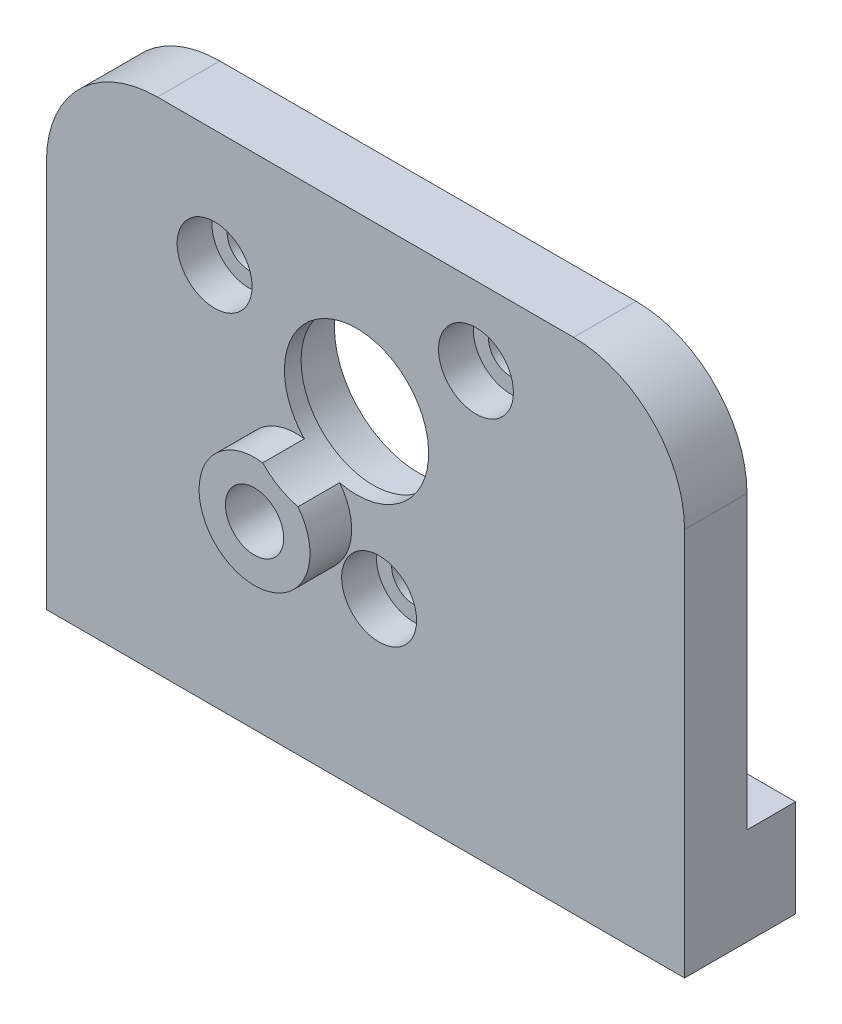
SolidWorks part; units mm, degrees
ref_plane "Front Plane" through (0, 0, 0) normal (0, 0, 1) x (1, 0, 0)
ref_plane "Top Plane" through (0, 0, 0) normal (0, 1, 0) x (1, 0, 0)
ref_plane "Right Plane" through (0, 0, 0) normal (1, 0, 0) x (0, 0, -1)
ref_plane "Plane1" through (0, 0, 4.5) normal (0, 0, 1) x (1, 0, 0)
sketch "Sketch1" plane through (0, 0, 4.5) normal (0, 0, 1) x (1, 0, 0)
  line L0 (-23, -18) -> (23, -18)
  line L1 (23, -18) -> (23, 18)
  line L2 (23, 18) -> (-23, 18)
  line L3 (-23, 18) -> (-23, -18)
extrude "Boss-Extrude1" add sketch "Sketch1" against normal blind 4.5
sketch "Sketch2" plane through (0, 0, 0) normal (0, 0, -1) x (-1, 0, 0)
  line L0 (-15, -11) -> (-15, -18)
  line L1 (-15, -18) -> (-23, -18)
  line L2 (-23, -18) -> (-23, -11)
  line L3 (-23, -11) -> (-15, -11)
extrude "Boss-Extrude2" add sketch "Sketch2" along normal blind 3.5
sketch "Sketch3" plane through (0, 0, 0) normal (0, 0, -1) x (-1, 0, 0)
  line L0 (23, -18) -> (15, -18)
  line L1 (15, -18) -> (15, -11)
  line L2 (15, -11) -> (23, -11)
  line L3 (23, -11) -> (23, -18)
extrude "Boss-Extrude3" add sketch "Sketch3" along normal blind 3.5
ref_plane "Plane2" through (0, -2, 0) normal (0, -1, 0) x (1, 0, 0)
sketch "Sketch4" plane through (0, -2, 0) normal (0, -1, 0) x (1, 0, 0)
  line L0 (-1, 7.5) -> (-5, 7.5)
  line L1 (-5, 7.5) -> (-5, 4.5)
  line L2 (-5, 4.5) -> (-1, 4.5)
  line L3 (-1, 4.5) -> (-1, 7.5)
  line L4 (-5, 7.5) -> (-5, 4.5) construction
revolve "Revolve1" add sketch "Sketch4" angle 360 about L4
hole_wizard "Ø1.7 (1.7) Diameter Hole1" positions "Sketch6" profile "Sketch5" hole size "Ø1.7" standard "ANSI Metric"
sketch "Sketch6" plane through (0, -18, 0) normal (0, -1, 0) x (-1, 0, 0)
  point P0 (0, -2.25)
sketch "Sketch5" plane through (0, -18, 2.25) normal (1, 0, 0) x (0, 0, -1)
  line L0 (0, 0) -> (0, 7.5107)
  line L1 (0, 7.5107) -> (0.85, 7)
  line L2 (0.85, 7) -> (0.85, 0)
  line L5 (0.85, 0) -> (0, 0)
  line L10 (0, 7.5107) -> (-0.85, 7) construction
  line L11 (0, -6.35) -> (0, 107.95) construction
  dimension "Hole Dia." = 1.7
  dimension "Hole Depth" = 7
  dimension "Drill Angle" = 118
hole_wizard "Ø2.5 (2.5) Diameter Hole1" positions "Sketch8" profile "Sketch7" hole size "Ø2.5" standard "ANSI Metric"
sketch "Sketch8" plane through (0, -18, 0) normal (0, -1, 0) x (-1, 0, 0)
  point P0 (-19, -0.5)
  point P1 (19, -0.5)
sketch "Sketch7" plane through (19, -18, 0.5) normal (1, 0, 0) x (0, 0, -1)
  line L0 (0, 0) -> (0, 6.7511)
  line L1 (0, 6.7511) -> (1.25, 6)
  line L2 (1.25, 6) -> (1.25, 0)
  line L5 (1.25, 0) -> (0, 0)
  line L10 (0, 6.7511) -> (-1.25, 6) construction
  line L11 (0, -6.35) -> (0, 107.95) construction
  dimension "Hole Dia." = 2.5
  dimension "Hole Depth" = 6
  dimension "Drill Angle" = 118
hole_wizard "Hole1" positions "Sketch10" profile "Sketch9" legacy end condition through all
sketch "Sketch10" plane through (0, 0, 0) normal (0, 0, -1) x (-1, 0, 0)
  point P0 (0.6458, 5.5417)
sketch "Sketch9" plane through (-0.6458, 5.5417, 0) normal (1, 0, 0) x (0, 1, 0)
  line L0 (0, 0) -> (0, 7.5)
  line L1 (0, 7.5) -> (5.2, 7.5)
  line L2 (5.2, 7.5) -> (5.2, 3.3)
  line L3 (5.2, 3.3) -> (6.1, 3.3)
  line L4 (6.1, 3.3) -> (6.1, 0)
  line L5 (6.1, 0) -> (0, 0)
  line L6 (0, 110) -> (0, -10) construction
  dimension "Diameter" = 10.4
  dimension "Depth" = 7.5
  dimension "C-Bore Diameter" = 12.2
  dimension "C-Bore Depth" = 3.3
hole_wizard "CBORE for M3 Hex Head Machine Screw1" positions "Sketch12" profile "Sketch11" counterbore size "M3" standard "ANSI Metric"
sketch "Sketch12" plane through (0, 0, 4.5) normal (0, 0, 1) x (1, 0, 0)
  point P0 (0.9801, -5.3374)
  point P1 (7.9629, 12.3894)
  point P2 (-10.8804, 9.5732)
sketch "Sketch11" plane through (0.9801, -5.3374, 4.5) normal (1, 0, 0) x (0, -1, 0)
  line L0 (0, 0) -> (0, 8)
  line L1 (0, 8) -> (1.6, 8)
  line L3 (1.6, 8) -> (1.6, 2.5)
  line L4 (1.6, 2.5) -> (2.7, 2.5)
  line L5 (2.7, 2.5) -> (2.7, 0)
  line L7 (2.7, 0) -> (0, 0)
  line L11 (0, -6.35) -> (0, 107.95) construction
  dimension "Thru Hole Dia." = 3.2
  dimension "Thru Hole Depth" = 8
  dimension "C'Bore Dia." = 5.4
  dimension "C'Bore Depth" = 2.5
hole_wizard "Ø4.2 (4.2) Diameter Hole1" positions "Sketch14" profile "Sketch13" hole size "Ø4.2" standard "ANSI Metric"
sketch "Sketch14" plane through (0, 0, 7.5) normal (0, 0, 1) x (1, 0, 0)
  point P0 (-5, -2)
sketch "Sketch13" plane through (-5, -2, 7.5) normal (1, 0, 0) x (0, -1, 0)
  line L0 (0, 0) -> (0, 7)
  line L1 (0, 7) -> (2.1, 7)
  line L2 (2.1, 7) -> (2.1, 0)
  line L5 (2.1, 0) -> (0, 0)
  line L10 (0, 7) -> (-2.1, 7) construction
  line L11 (0, -6.35) -> (0, 107.95) construction
  dimension "Hole Dia." = 4.2
  dimension "Hole Depth" = 7
  dimension "Drill Angle" = 180
fillet "Fillet1" radius 3 2 edges at (-15, -11, -1.75) (15, -11, -1.75)
fillet "Fillet2" radius 8 2 edges at (-23, 18, 2.25) (23, 18, 2.25)
